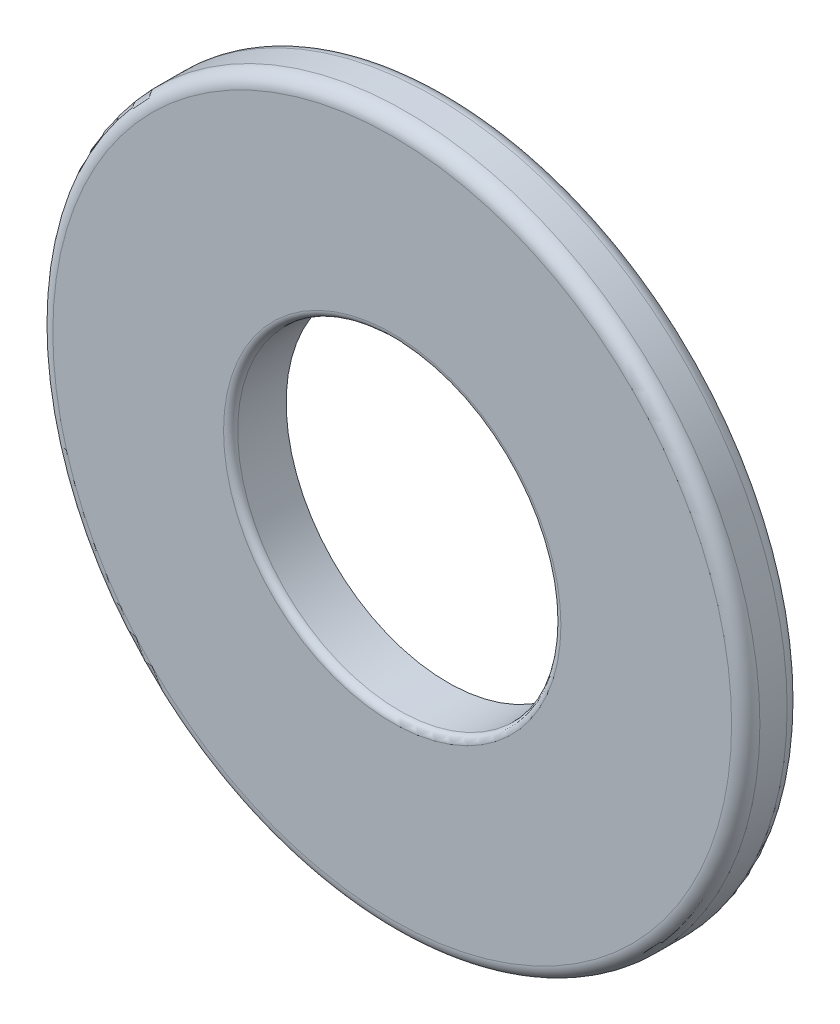
SolidWorks part; units mm, degrees
ref_plane "Front Plane" through (0, 0, 0) normal (0, 0, 1) x (1, 0, 0)
ref_plane "Top Plane" through (0, 0, 0) normal (0, 1, 0) x (1, 0, 0)
ref_plane "Right Plane" through (0, 0, 0) normal (1, 0, 0) x (0, 0, -1)
sketch "Sketch1" plane through (0, 0, 0) normal (0, 0, 1) x (1, 0, 0)
  circle A0 centre (0, 0) radius 3.5 construction
  circle A1 centre (0, 0) radius 1.6 construction
  point P5 (0, -3.5)
  dimension "OD" = 7
  dimension "ID" = 3.2
sketch "Sketch2" plane through (0, 0, 0) normal (1, 0, 0) x (0, 0, -1)
  line L0 (0.225, 0) -> (-0.225, 0) construction
  line L1 (-0.275, -3.5) -> (0.275, -3.5) construction
  point P0 (-0.275, -3.5)
  point P3 (0.275, -3.5)
  point P4 (0, 0)
  point P9 (0, -3.5)
  point P10 (0.225, -3.5)
  point P11 (-0.275, -3.5)
  point P12 (-0.225, -3.5)
  point P13 (0.275, -3.5)
  dimension "Thickness Range [Min]" = 0.45
  dimension "Thickness Range [Max]" = 0.55
sketch "Sketch3" plane through (0, 0, 0) normal (0, 0, 1) x (1, 0, 0)
  circle A0 centre (0, 0) radius 1.6 construction
  circle A1 centre (0, 0) radius 3.5 construction
  circle A2 centre (0, 0) radius 1.6
  circle A3 centre (0, 0) radius 3.5
extrude "Boss-Extrude1" add sketch "Sketch3" against normal up to vertex (0.275 mm away) and the other way up to vertex (0.275 mm away) up to point (0, -3.5, -0.275) other way up to point (0, -3.5, 0.275)
fillet "Fillet1" radius 0.14 2 edges at (3.5, 0, -0.275) (3.5, 0, 0.275)
fillet "Fillet2" radius 0.07 1 edges at (1.6, 0, 0.275)
equation "\"D1@Fillet1\"=\"OD@Sketch1\"*.02"
equation "\"D1@Fillet2\"=\"OD@Sketch1\"*.01"
